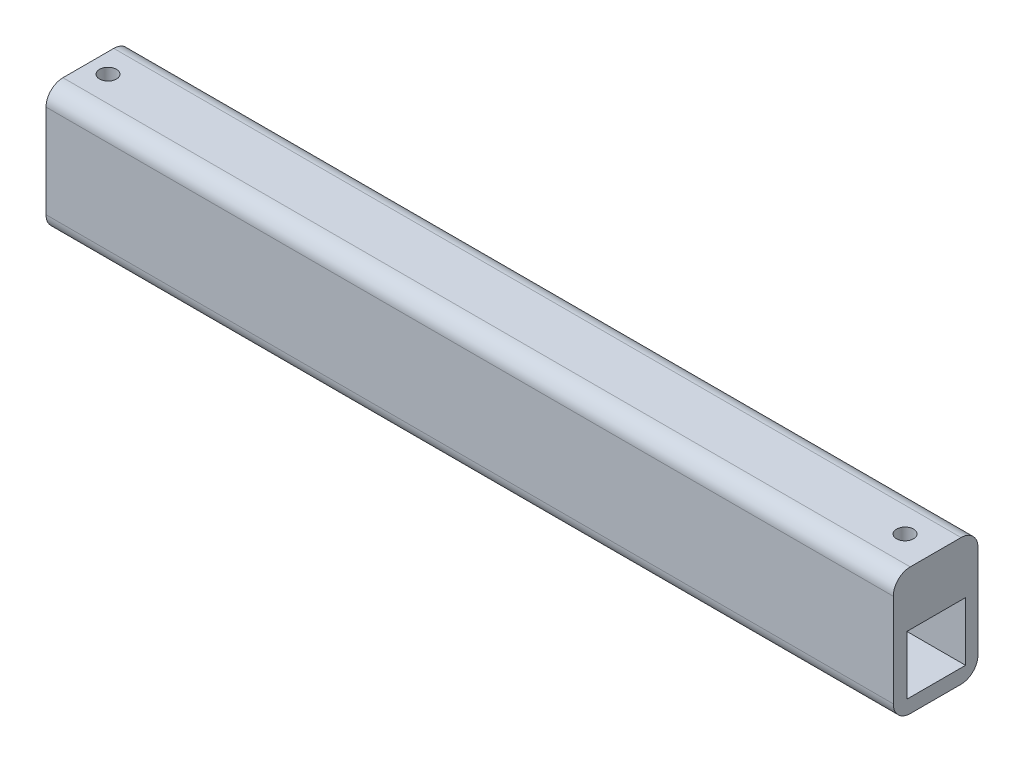
SolidWorks part; units mm, degrees
ref_plane "Front Plane" through (0, 0, 0) normal (0, 0, 1) x (1, 0, 0)
ref_plane "Top Plane" through (0, 0, 0) normal (0, 1, 0) x (1, 0, 0)
ref_plane "Right Plane" through (0, 0, 0) normal (1, 0, 0) x (0, 0, -1)
sketch "Sketch1" plane through (0, 0, 0) normal (0, 0, 1) x (1, 0, 0)
  line L1 (-89.2449, 8.833) -> (110.7551, 8.833)
  line L2 (-89.2449, 8.833) -> (-89.2449, -21.167)
  line L3 (-89.2449, -21.167) -> (110.7551, -21.167)
  line L4 (110.7551, 8.833) -> (110.7551, -21.167)
  dimension "D1" = 200
  dimension "D2" = 30
extrude "Boss-Extrude1" add sketch "Sketch1" along normal blind 20
fillet "Fillet8" radius 4 4 edges at (10.7551, -21.167, 0) (10.7551, -21.167, 20) (10.7551, 8.833, 20) (10.7551, 8.833, 0)
sketch "Sketch3" plane through (-89.2449, 0, 0) normal (-1, 0, 0) x (0, 0, 1)
  line L1 (2.9397, -3.9698) -> (16.8169, -3.9698)
  line L2 (2.9397, -3.9698) -> (2.9397, -17.8165)
  line L3 (2.9397, -17.8165) -> (16.8169, -17.8165)
  line L4 (16.8169, -3.9698) -> (16.8169, -17.8165)
extrude "Cut-Extrude1" cut sketch "Sketch3" against normal blind 200
sketch "Sketch4" plane through (0, 8.833, 0) normal (0, 1, 0) x (1, 0, 0)
  circle A0 centre (-84.6471, -9.9604) radius 2
  point P2 (0, 0)
  dimension "D1" = 4
extrude "Cut-Extrude2" cut sketch "Sketch4" against normal blind 20
sketch "Sketch5" plane through (0, 8.833, 0) normal (0, 1, 0) x (1, 0, 0)
  circle A0 centre (103.4083, -9.8824) radius 2
  dimension "D1" = 4
extrude "Cut-Extrude3" cut sketch "Sketch5" against normal blind 20
ref_plane "Plane2" through (-89.2449, 8.833, 16) normal (0, 0, -1) x (-1, 0, 0)
